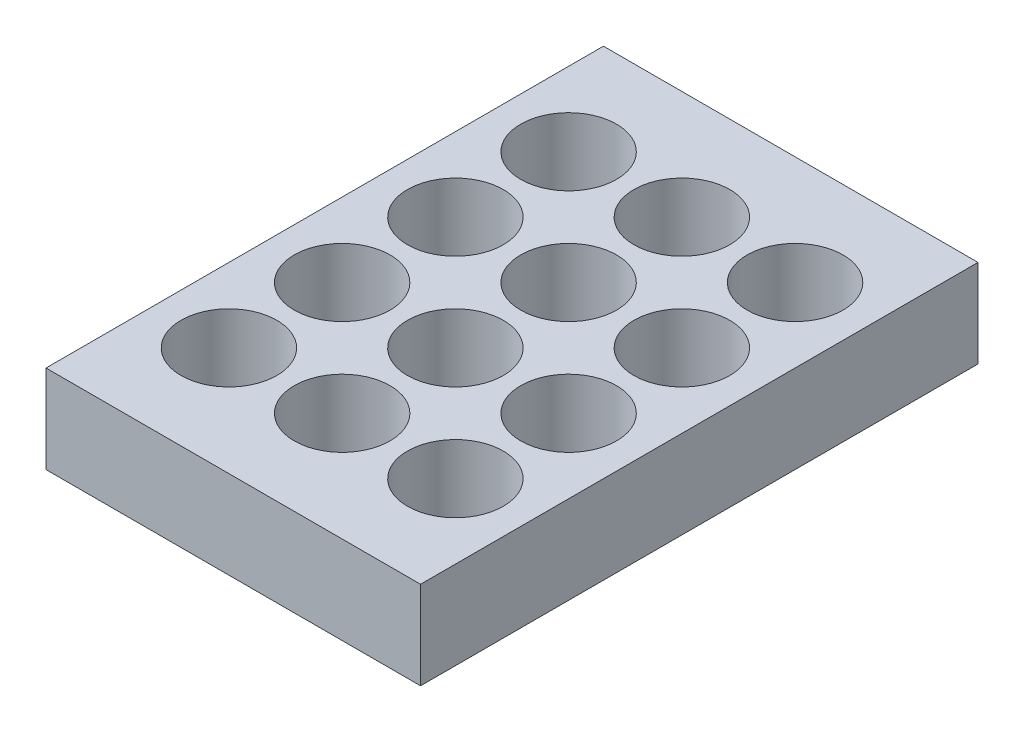
SolidWorks part; units mm, degrees
ref_plane "Front" through (0, 0, 0) normal (0, 0, 1) x (1, 0, 0)
ref_plane "Top" through (0, 0, 0) normal (0, 1, 0) x (1, 0, 0)
ref_plane "Right" through (0, 0, 0) normal (1, 0, 0) x (0, 0, -1)
sketch "Sketch1" plane through (0, 0, 0) normal (0, 1, 0) x (1, 0, 0)
  line L1 (0, 0) -> (86, 0)
  line L2 (0, 0) -> (0, 128)
  line L3 (0, 128) -> (86, 128)
  line L4 (86, 0) -> (86, 128)
  dimension "D1" = 86
  dimension "D2" = 128
extrude "Boss-Extrude1" add sketch "Sketch1" along normal blind 20.2
sketch "Sketch2" plane through (0, 20.2, 0) normal (0, 1, 0) x (1, 0, 0)
  line L1 (0, 128) -> (0, 0) construction
  line L2 (0, 0) -> (86, 0) construction
  circle A0 centre (17, 25) radius 11
  dimension "D1" = 22
  dimension "D2" = 17
  dimension "D3" = 25
extrude "Cut-Extrude1" cut sketch "Sketch2" against normal blind 17.7
pattern_linear "LPattern3" count 4 spacing 26 along (0, 0, -1) count 3 spacing 26 along (1, 0, 0) of "Cut-Extrude1"
equation "\"D2@Sketch2\"=6+\"D1@Sketch2\"/2"
equation "\"D3@Sketch2\"=14+\"D1@Sketch2\"/2"
